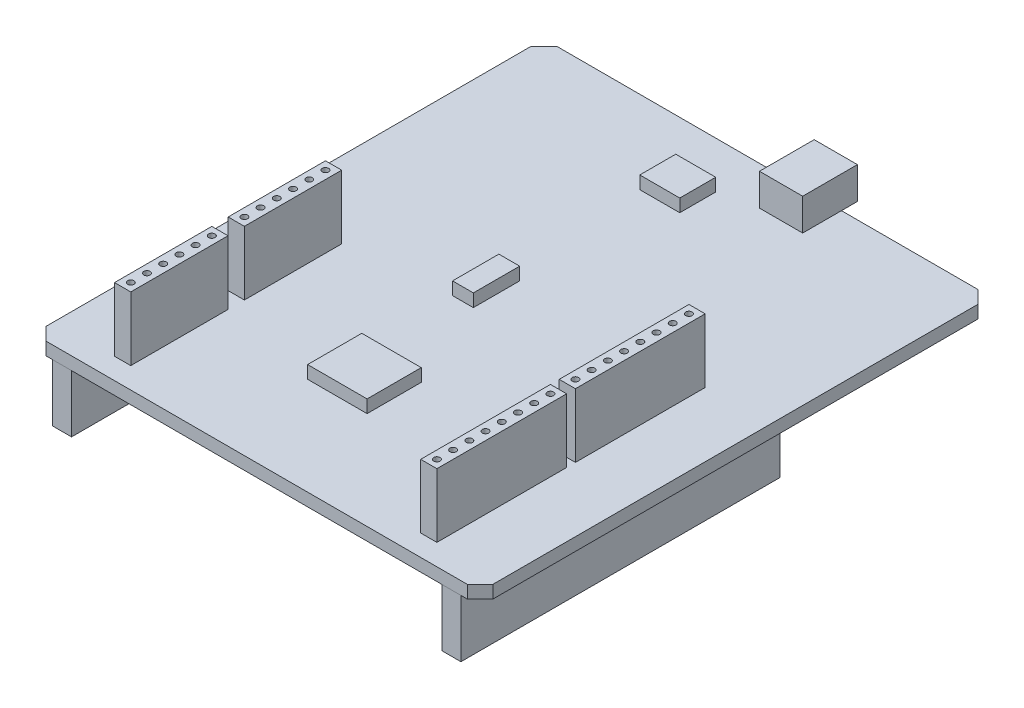
SolidWorks part; units mm, degrees
ref_plane "Front Plane" through (0, 0, 0) normal (0, 0, 1) x (1, 0, 0)
ref_plane "Top Plane" through (0, 0, 0) normal (0, 1, 0) x (1, 0, 0)
ref_plane "Right Plane" through (0, 0, 0) normal (1, 0, 0) x (0, 0, -1)
sketch "Sketch1" plane through (0, 0, 0) normal (0, 1, 0) x (1, 0, 0)
  line L1 (-76.1915, 102.4862) -> (-6.1915, 102.4862)
  line L2 (-76.1915, 102.4862) -> (-76.1915, 22.4862)
  line L3 (-76.1915, 22.4862) -> (-6.1915, 22.4862)
  line L4 (-6.1915, 102.4862) -> (-6.1915, 22.4862)
  dimension "D1" = 70
  dimension "D2" = 80
extrude "Boss-Extrude1" add sketch "Sketch1" along normal blind 2
sketch "Sketch3" plane through (0, 0, -22.4862) normal (0, 0, 1) x (1, 0, 0)
  line L1 (-76.1915, 0) -> (-6.1915, 0)
  line L2 (-76.1915, 0) -> (-76.1915, 2)
  line L3 (-76.1915, 2) -> (-6.1915, 2)
  line L4 (-6.1915, 0) -> (-6.1915, 2)
  line L5 (-9.1915, 0) -> (-12.1915, 0)
  line L6 (-9.1915, 0) -> (-9.1915, -9)
  line L7 (-9.1915, -9) -> (-12.1915, -9)
  line L8 (-12.1915, 0) -> (-12.1915, -9)
  line L9 (-73.1915, 0) -> (-70.1915, 0)
  line L10 (-73.1915, 0) -> (-73.1915, -9)
  line L11 (-73.1915, -9) -> (-70.1915, -9)
  line L12 (-70.1915, 0) -> (-70.1915, -9)
  dimension "D1" = 3
  dimension "D2" = 3
  dimension "D3" = 9
  dimension "D4" = 3
extrude "Boss-Extrude4" add sketch "Sketch3" against normal blind 50 separate body contours L12 L1 L10 L11 | L1 L8 L7 L6
sketch "Sketch2" plane through (0, 2, 0) normal (0, 1, 0) x (1, 0, 0)
  line L0 (-76.1915, 102.4862) -> (-76.1915, 22.4862) construction
  line L1 (-68.1915, 87.4862) -> (-14.1915, 87.4862)
  line L2 (-68.1915, 87.4862) -> (-68.1915, 23.4862)
  line L3 (-68.1915, 23.4862) -> (-14.1915, 23.4862)
  line L4 (-14.1915, 87.4862) -> (-14.1915, 23.4862)
  line L5 (-6.1915, 22.4862) -> (-6.1915, 102.4862) construction
  line L6 (-76.1915, 22.4862) -> (-6.1915, 22.4862) construction
  line L7 (-6.1915, 102.4862) -> (-76.1915, 102.4862) construction
  line L8 (-17.5352, 67.8176) -> (-17.5352, 47.4976) construction
  line L9 (-66.7652, 58.8376) -> (-66.7652, 43.5976)
  line L10 (-66.7652, 58.8376) -> (-64.2252, 58.8376)
  line L11 (-64.2252, 58.8376) -> (-64.2252, 43.5976)
  line L12 (-66.7652, 43.5976) -> (-64.2252, 43.5976)
  line L13 (-66.7652, 41.0376) -> (-66.7652, 25.7976)
  line L14 (-66.7652, 41.0376) -> (-64.2252, 41.0376)
  line L15 (-64.2252, 41.0376) -> (-64.2252, 25.7976)
  line L16 (-66.7652, 25.7976) -> (-64.2252, 25.7976)
  line L17 (-18.8052, 67.8176) -> (-18.8052, 47.4976)
  line L18 (-18.8052, 67.8176) -> (-16.2652, 67.8176)
  line L19 (-16.2652, 67.8176) -> (-16.2652, 47.4976)
  line L20 (-18.8052, 47.4976) -> (-16.2652, 47.4976)
  line L21 (-18.8052, 46.1176) -> (-18.8052, 25.7976)
  line L22 (-18.8052, 46.1176) -> (-16.2652, 46.1176)
  line L23 (-16.2652, 46.1176) -> (-16.2652, 25.7976)
  line L24 (-18.8052, 25.7976) -> (-16.2652, 25.7976)
  circle A0 centre (-17.5352, 66.5476) radius 0.5
  circle A1 centre (-17.5352, 64.0076) radius 0.5
  circle A2 centre (-17.5352, 61.4676) radius 0.5
  circle A3 centre (-17.5352, 58.9276) radius 0.5
  circle A4 centre (-17.5352, 56.3876) radius 0.5
  circle A5 centre (-17.5352, 53.8476) radius 0.5
  circle A6 centre (-17.5352, 51.3076) radius 0.5
  circle A7 centre (-17.5352, 48.7676) radius 0.5
  circle A8 centre (-17.5352, 44.8476) radius 0.5
  circle A9 centre (-65.4952, 57.5676) radius 0.5
  circle A10 centre (-65.4952, 39.7676) radius 0.5
  circle A11 centre (-17.5352, 42.3076) radius 0.5
  circle A12 centre (-17.5352, 39.7676) radius 0.5
  circle A13 centre (-17.5352, 37.2276) radius 0.5
  circle A14 centre (-17.5352, 34.6876) radius 0.5
  circle A15 centre (-17.5352, 32.1476) radius 0.5
  circle A16 centre (-17.5352, 29.6076) radius 0.5
  circle A17 centre (-17.5352, 27.0676) radius 0.5
  circle A18 centre (-65.4952, 55.0276) radius 0.5
  circle A19 centre (-65.4952, 37.2276) radius 0.5
  circle A20 centre (-65.4952, 52.4876) radius 0.5
  circle A21 centre (-65.4952, 34.6876) radius 0.5
  circle A22 centre (-65.4952, 49.9476) radius 0.5
  circle A23 centre (-65.4952, 32.1476) radius 0.5
  circle A24 centre (-65.4952, 47.4076) radius 0.5
  circle A25 centre (-65.4952, 29.6076) radius 0.5
  circle A26 centre (-65.4952, 44.8676) radius 0.5
  circle A27 centre (-65.4952, 27.0676) radius 0.5
  point P32 (-65.4952, 58.8376)
  point P53 (-65.4952, 41.0376)
  dimension "D16" = 1
  dimension "D17" = 1
  dimension "D18" = 1
  dimension "D19" = 1
  dimension "D1" = 8
  dimension "D2" = 8
  dimension "D3" = 1
  dimension "D4" = 15
  dimension "D5" = 2.54
  dimension "D6" = 2.54
  dimension "D7" = 20.32
  dimension "D8" = 1.38
  dimension "D9" = 2.56
  dimension "D10" = 45.42
  dimension "D11" = 15.24
  dimension "D12" = 1.27
  dimension "D13" = 1.27
  dimension "D14" = 1.27
  dimension "D15" = 1.27
extrude "Boss-Extrude5" add sketch "Sketch2" along normal blind 10 contours L13 L16 L15 L14 A27 A25 A23 A21 A19 A10 | L9 L12 L11 L10 A26 A24 A22 A20 A18 A9 | L21 L24 L23 L22 A17 A16 A15 A14 A13 A12 A11 A8 | L18 L8 A0 A1 A2 A3 A4 A5 A6 A7 L20 L19 | L8 L18 L17 L20 A7 A6 A5 A4 A3 A2 A1 A0
sketch "Sketch4" plane through (0, 2, 0) normal (0, 1, 0) x (1, 0, 0)
  line L1 (-29.5805, 96.4114) -> (-36.3532, 96.4114)
  line L2 (-29.5805, 96.4114) -> (-29.5805, 104.9848)
  line L3 (-29.5805, 104.9848) -> (-36.3532, 104.9848)
  line L4 (-36.3532, 96.4114) -> (-36.3532, 104.9848)
extrude "Boss-Extrude6" add sketch "Sketch4" along normal blind 5
sketch "Sketch5" plane through (0, 2, 0) normal (0, 1, 0) x (1, 0, 0)
  line L1 (-39.2017, 37.7948) -> (-48.5178, 37.7948)
  line L2 (-39.2017, 37.7948) -> (-39.2017, 46.2803)
  line L3 (-39.2017, 46.2803) -> (-48.5178, 46.2803)
  line L4 (-48.5178, 37.7948) -> (-48.5178, 46.2803)
  line L5 (-45.2593, 60.4985) -> (-48.5178, 60.4985)
  line L6 (-45.2593, 60.4985) -> (-45.2593, 67.7568)
  line L7 (-45.2593, 67.7568) -> (-48.5178, 67.7568)
  line L8 (-48.5178, 60.4985) -> (-48.5178, 67.7568)
  line L9 (-41.9642, 89.5381) -> (-48.2232, 89.5381)
  line L10 (-41.9642, 89.5381) -> (-41.9642, 95.1728)
  line L11 (-41.9642, 95.1728) -> (-48.2232, 95.1728)
  line L12 (-48.2232, 89.5381) -> (-48.2232, 95.1728)
extrude "Boss-Extrude7" add sketch "Sketch5" along normal blind 2
chamfer "Chamfer1" distance 2 angle 45 4 edges at (-76.1915, 1, -102.4862) (-76.1915, 1, -22.4862) (-6.1915, 1, -102.4862) (-6.1915, 1, -22.4862)
